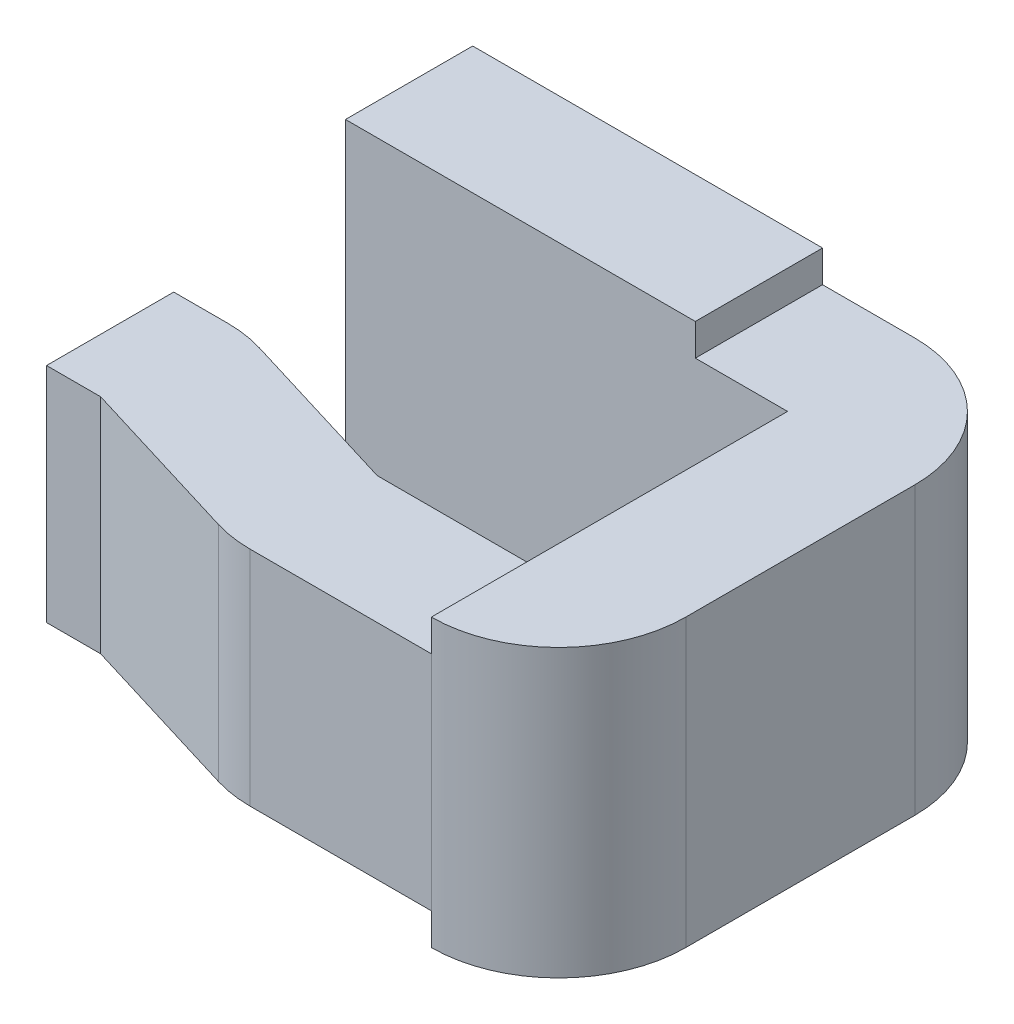
SolidWorks part; units mm, degrees
ref_plane "Front Plane" through (0, 0, 0) normal (0, 0, 1) x (1, 0, 0)
ref_plane "Top Plane" through (0, 0, 0) normal (0, 1, 0) x (1, 0, 0)
ref_plane "Right Plane" through (0, 0, 0) normal (1, 0, 0) x (0, 0, -1)
sketch "Sketch1" plane through (0, 0, 0) normal (0, 1, 0) x (1, 0, 0)
  line L0 (0, 0) -> (1.39, 0) construction
  line L1 (1.59, -0.2) -> (1.59, -0.92) construction
  line L2 (1.39, -1.12) -> (0.8198, -1.12) construction
  line L3 (0.7615, -1.1113) -> (0.2285, -0.9487) construction
  line L4 (0.1702, -0.94) -> (0, -0.94) construction
  line L5 (0, -0.2) -> (1.39, -0.2)
  line L6 (1.39, -0.2) -> (1.39, -0.92)
  line L7 (1.39, -0.92) -> (0.8198, -0.92)
  line L8 (0.8198, -0.92) -> (0.2869, -0.7574)
  line L9 (0.1702, -0.74) -> (0, -0.74)
  line L10 (0, 0.2) -> (1.39, 0.2)
  line L11 (1.79, -0.2) -> (1.79, -0.92)
  line L12 (1.39, -1.32) -> (0.8198, -1.32)
  line L13 (0.7031, -1.3026) -> (0.1702, -1.14)
  line L14 (0.1702, -1.14) -> (0, -1.14)
  line L15 (0, -0.2) -> (0, 0.2)
  line L16 (0, -0.74) -> (0, -1.14)
  arc A0 (0.2285, -0.9487) -> (0.1702, -0.94) centre (0.1702, -1.14) ccw construction
  arc A1 (0.8198, -1.12) -> (0.7615, -1.1113) centre (0.8198, -0.92) cw construction
  arc A2 (1.59, -0.92) -> (1.39, -1.12) centre (1.39, -0.92) cw construction
  arc A3 (1.39, 0) -> (1.59, -0.2) centre (1.39, -0.2) cw construction
  arc A4 (1.39, -0.2) -> (1.39, -0.2) centre (1.39, -0.2) cw
  arc A5 (1.39, -0.92) -> (1.39, -0.92) centre (1.39, -0.92) cw
  arc A6 (0.8198, -0.92) -> (0.8198, -0.92) centre (0.8198, -0.92) cw
  arc A7 (0.2869, -0.7574) -> (0.1702, -0.74) centre (0.1702, -1.14) ccw
  arc A8 (1.39, 0.2) -> (1.79, -0.2) centre (1.39, -0.2) cw
  arc A9 (1.79, -0.92) -> (1.39, -1.32) centre (1.39, -0.92) cw
  arc A10 (0.8198, -1.32) -> (0.7031, -1.3026) centre (0.8198, -0.92) cw
  arc A11 (0.1702, -1.14) -> (0.1702, -1.14) centre (0.1702, -1.14) ccw
  point P3 (0.199, -0.54)
  point P8 (0.1156, -0.54)
  point P9 (0.0747, -0.54)
  point P10 (0, 0)
  point P13 (0.2, -0.94)
  point P16 (0.79, -1.12)
  point P19 (1.59, -1.12)
  point P22 (1.59, 0)
  dimension "D6" = 0.2
  dimension "D1" = 1.59
  dimension "D2" = 0.18
  dimension "D3" = 0.94
  dimension "D4" = 0.8
  dimension "D5" = 0.2
  dimension "D7" = 0.2
  dimension "D8" = 0.2
extrude "Boss-Extrude1" add sketch "Sketch1" along normal mid plane 1.1
sketch "Sketch4" plane through (0, 0, -0.2) normal (0, 0, -1) x (-1, 0, 0)
  line L0 (-1.39, 0.55) -> (0, 0.55) construction
  line L1 (-1.1, 0.55) -> (-2.4096, 0.55)
  line L2 (-1.1, 0.55) -> (-1.1, 0.45)
  line L3 (-1.1, 0.45) -> (-2.4096, 0.45)
  line L4 (-2.4096, 0.55) -> (-2.4096, 0.45)
  line L5 (0, 0.55) -> (0, -0.55) construction
  line L6 (0.836, 0) -> (-0.836, 0) construction
  point P8 (-1.1, 0.5)
  dimension "D1" = 1.1
  dimension "D2" = 0.45
extrude "Cut-Extrude1" cut sketch "Sketch4" against normal through all
mirror "Mirror1" about plane through (0, 0, 0) normal (0, 1, 0) of "Cut-Extrude1"
sketch "Sketch5" plane through (0, 0, 0.74) normal (0, 0, -1) x (-1, 0, 0)
  line L0 (0, 0.55) -> (0, -0.55) construction
  line L1 (0, 0.35) -> (-1.39, 0.35)
  line L2 (0, 0.35) -> (0, 1.3331)
  line L3 (0, 1.3331) -> (-1.39, 1.3331)
  line L4 (-1.39, 0.35) -> (-1.39, 1.3331)
  line L5 (-1.39, 0.45) -> (-1.39, -0.45) construction
  line L6 (0.836, 0) -> (-0.836, 0) construction
  dimension "D1" = 0.35
extrude "Cut-Extrude2" cut sketch "Sketch5" against normal through all
mirror "Mirror2" about plane through (0, 0, 0) normal (0, 1, 0) of "Cut-Extrude2"
